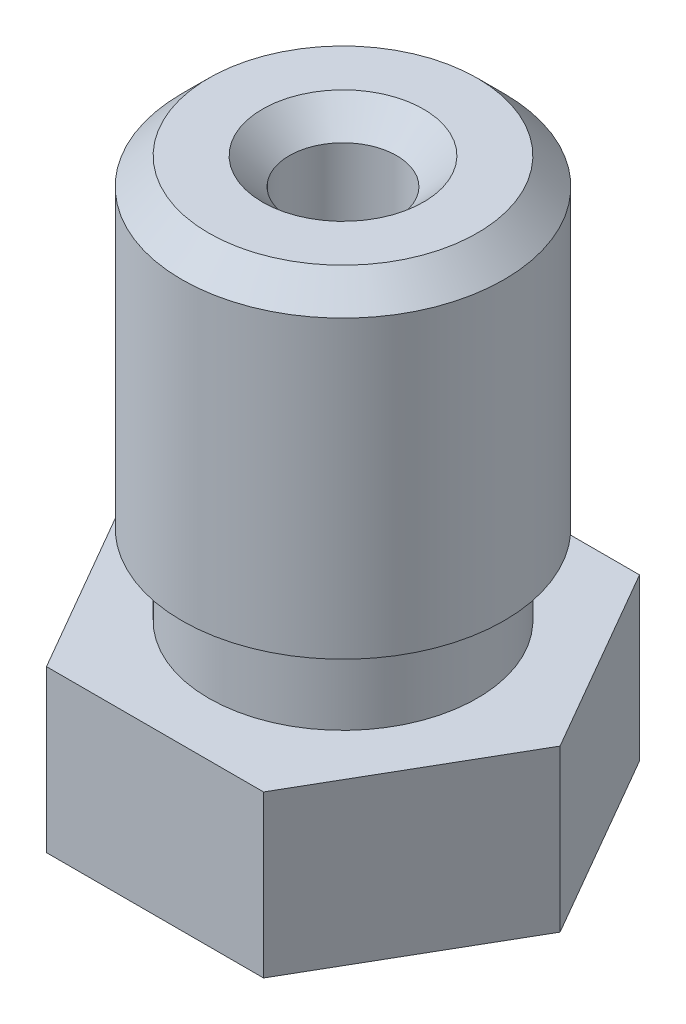
SolidWorks part; units mm, degrees
material "Brass"
ref_plane "Front Plane" through (0, 0, 0) normal (0, 0, 1) x (1, 0, 0)
ref_plane "Top Plane" through (0, 0, 0) normal (0, 1, 0) x (1, 0, 0)
ref_plane "Right Plane" through (0, 0, 0) normal (1, 0, 0) x (0, 0, -1)
ref_plane "Plane1" through (0, 0, 0) normal (0, -1, 0) x (1, 0, 0)
sketch "Sketch1" plane through (0, 0, 0) normal (0, -1, 0) x (1, 0, 0)
  line L0 (-2.0207, 3.5) -> (-4.0415, 0)
  line L1 (-4.0415, 0) -> (-2.0207, -3.5)
  line L2 (-2.0207, -3.5) -> (2.0207, -3.5)
  line L3 (2.0207, -3.5) -> (4.0415, 0)
  line L4 (4.0415, 0) -> (2.0207, 3.5)
  line L5 (2.0207, 3.5) -> (-2.0207, 3.5)
extrude "Boss-Extrude1" add sketch "Sketch1" against normal blind 3
ref_plane "Plane2" through (0, 0, 0) normal (0, 0, -1) x (-1, 0, 0)
sketch "Sketch2" plane through (0, 0, 0) normal (0, 0, -1) x (-1, 0, 0)
  line L0 (-2.5, 3) -> (0, 3)
  line L1 (0, 3) -> (0, 10.5)
  line L2 (0, 10.5) -> (-3, 10.5)
  line L3 (-3, 10.5) -> (-3, 4.5)
  line L4 (-3, 4.5) -> (-2.5, 4.5)
  line L5 (-2.5, 4.5) -> (-2.5, 3)
  line L6 (0, 3) -> (0, 10.5) construction
revolve "Revolve1" add sketch "Sketch2" angle 360 about L6
sketch "Sketch3" plane through (0, 0, 0) normal (0, 0, 1) x (1, 0, 0)
  line L0 (2.5, 0) -> (0, 0)
  line L1 (0, 0) -> (0, -2)
  line L2 (0, -2) -> (0.5, -2)
  line L3 (0.5, -2) -> (2.5, 0)
  line L4 (0, 0) -> (0, -2) construction
revolve "Revolve2" add sketch "Sketch3" angle 360 about L4
sketch "Sketch4" plane through (0, 0, 0) normal (0, 0, -1) x (-1, 0, 0)
  line L0 (-0.25, -2) -> (0, -2)
  line L1 (0, -2) -> (0, 10.5)
  line L2 (0, 10.5) -> (-1, 10.5)
  line L3 (-1, 10.5) -> (-1, 0)
  line L4 (-1, 0) -> (-0.75, -0.2273)
  line L5 (-0.75, -0.2273) -> (-0.75, -0.7)
  line L6 (-0.75, -0.7) -> (-0.25, -1.2)
  line L7 (-0.25, -1.2) -> (-0.25, -2)
  line L8 (0, -2) -> (0, 10.5) construction
  dimension "D1" = 1
  dimension "D2" = 0.25
  dimension "D3" = 0.75
  dimension "D4" = 0.5
  dimension "D5" = 0.8
  dimension "D6" = 0.2273
  dimension "D7" = 0.4727
revolve "Cut-Revolve1" cut sketch "Sketch4" angle 360 about L8
chamfer "Chamfer1" distance 0.5 angle 45 2 edges at (0, 10.5, 3) (0, 10.5, 1)
